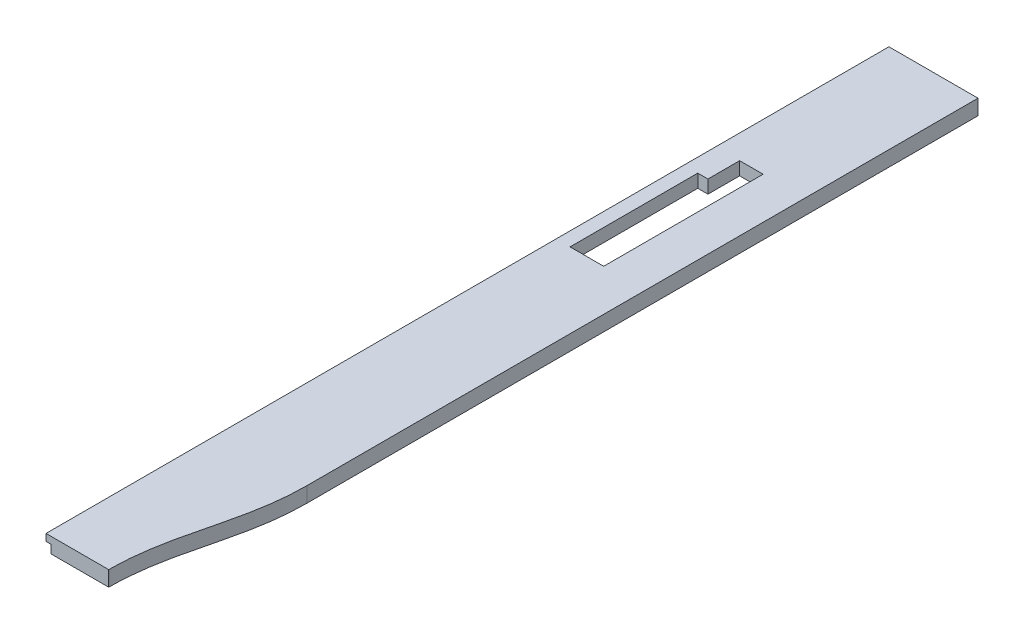
SolidWorks part; units mm, degrees
ref_plane "Plan de face" through (0, 0, 0) normal (0, 0, 1) x (1, 0, 0)
ref_plane "Plan de dessus" through (0, 0, 0) normal (0, 1, 0) x (1, 0, 0)
ref_plane "Plan de droite" through (0, 0, 0) normal (1, 0, 0) x (0, 0, -1)
sketch "Esquisse1" plane through (0, 0, 0) normal (0, 0, 1) x (1, 0, 0)
  line L0 (128.5, -500) -> (128.5, -490) construction
  line L1 (0, -484) -> (128.5, -484)
  line L2 (0, -484) -> (0, -506)
  line L3 (0, -506) -> (128.5, -506)
  line L4 (128.5, -484) -> (128.5, -506)
  line L5 (122.5, -506) -> (0, -506) construction
ref_plane "Plan1" through (122.5, -506, 0) normal (-1, 0, 0) x (0, 0, 1)
extrude "Boss.-Extru.1" add sketch "Esquisse1" along normal up to surface (1216 mm away) contours L3 L4 L1 L2
sketch "Esquisse4" plane through (0, -484, 0) normal (0, 1, 0) x (1, 0, 0)
  line L0 (128.5, -1216) -> (128.5, 0) construction
  line L1 (90.5, -191.4612) -> (90.5, -192.2938) construction
  line L2 (128.5, -236.915) -> (128.5, -244.4742) construction
  line L4 (128.5, -1216) -> (0, -1216) construction
  line L5 (90.5, -1215.9) -> (90.5, -1216)
  line L6 (90.5, -1216) -> (128.5, -1216)
  line L7 (128.5, -1216) -> (128.5, -968)
  spline S0 degree 3 poles (128.5, -968) (128.5, -1061.3333) (90.5, -1122.5667) (90.5, -1215.9) knots 0 0 0 0 1 1 1 1
  dimension "D2" = 280
  dimension "D3" = 280
  dimension "D1" = 0.1
  dimension "D4" = 12
  dimension "D5" = 10
extrude "Enlèv. mat.-Extru.1" cut sketch "Esquisse4" against normal through all
sketch "Esquisse5" plane through (0, 0, 0) normal (-1, 0, 0) x (0, 0, 1)
  line L0 (1216, -506) -> (0, -506) construction
  line L1 (1216, -990) -> (1216, -980) construction
  line L2 (1004, -506) -> (1216, -506)
  line L3 (1004, -506) -> (1004, -494)
  line L4 (1004, -494) -> (1216, -494)
  line L5 (1216, -506) -> (1216, -494)
  line L6 (1016, -968) -> (1016, -506) construction
  dimension "D1" = 12
  dimension "D2" = 12
extrude "Enlèv. mat.-Extru.2" cut sketch "Esquisse5" against normal blind 7
sketch "Esquisse6" plane through (0, -506, 0) normal (0, -1, 0) x (1, 0, 0)
  line L4 (10, 480) -> (10, 250)
  line L5 (20, 240) -> (68.5, 240)
  line L6 (78.5, 250) -> (78.5, 480)
  line L7 (68.5, 490) -> (20, 490)
  line L8 (10, 480) -> (10, 250)
  line L9 (20, 240) -> (68.5, 240)
  line L10 (78.5, 250) -> (78.5, 480)
  line L11 (68.5, 490) -> (20, 490)
  arc A4 (20, 490) -> (10, 480) centre (20, 480) ccw
  arc A5 (10, 250) -> (20, 240) centre (20, 250) ccw
  arc A6 (68.5, 240) -> (78.5, 250) centre (68.5, 250) ccw
  arc A7 (78.5, 480) -> (68.5, 490) centre (68.5, 480) ccw
  arc A8 (20, 490) -> (10, 480) centre (20, 480) ccw
  arc A9 (10, 250) -> (20, 240) centre (20, 250) ccw
  arc A10 (68.5, 240) -> (78.5, 250) centre (68.5, 250) ccw
  arc A11 (78.5, 480) -> (68.5, 490) centre (68.5, 480) ccw
  dimension "D1" = 0
extrude "Enlèv. mat.-Extru.3" cut sketch "Esquisse6" against normal blind 3
ref_plane "Plan2" through (10, -506, 480) normal (0, 0, -1) x (-1, 0, 0)
sketch "Esquisse11" plane through (0, -503, 0) normal (0, -1, 0) x (1, 0, 0)
  line L0 (68.5, 480) -> (20, 480)
  line L1 (20, 480) -> (20, 295.75)
  line L2 (20, 295.75) -> (34.65, 295.75)
  line L3 (34.65, 295.75) -> (34.65, 250)
  line L4 (34.65, 250) -> (68.5, 250)
  line L5 (68.5, 250) -> (68.5, 480)
  line L6 (68.5, 490) -> (20, 490) construction
  line L7 (78.5, 250) -> (78.5, 480) construction
  line L8 (10, 480) -> (10, 250) construction
  line L9 (20, 240) -> (68.5, 240) construction
  line L10 (36.25, 283.75) -> (36.25, 277.75) construction
  circle A0 centre (38, 309.75) radius 9.5 construction
  dimension "D1" = 10
  dimension "D2" = 10
  dimension "D3" = 10
  dimension "D4" = 10
  dimension "D5" = 1.6
  dimension "D6" = 14
extrude "Enlèv. mat.-Extru.4" cut sketch "Esquisse11" against normal through all
